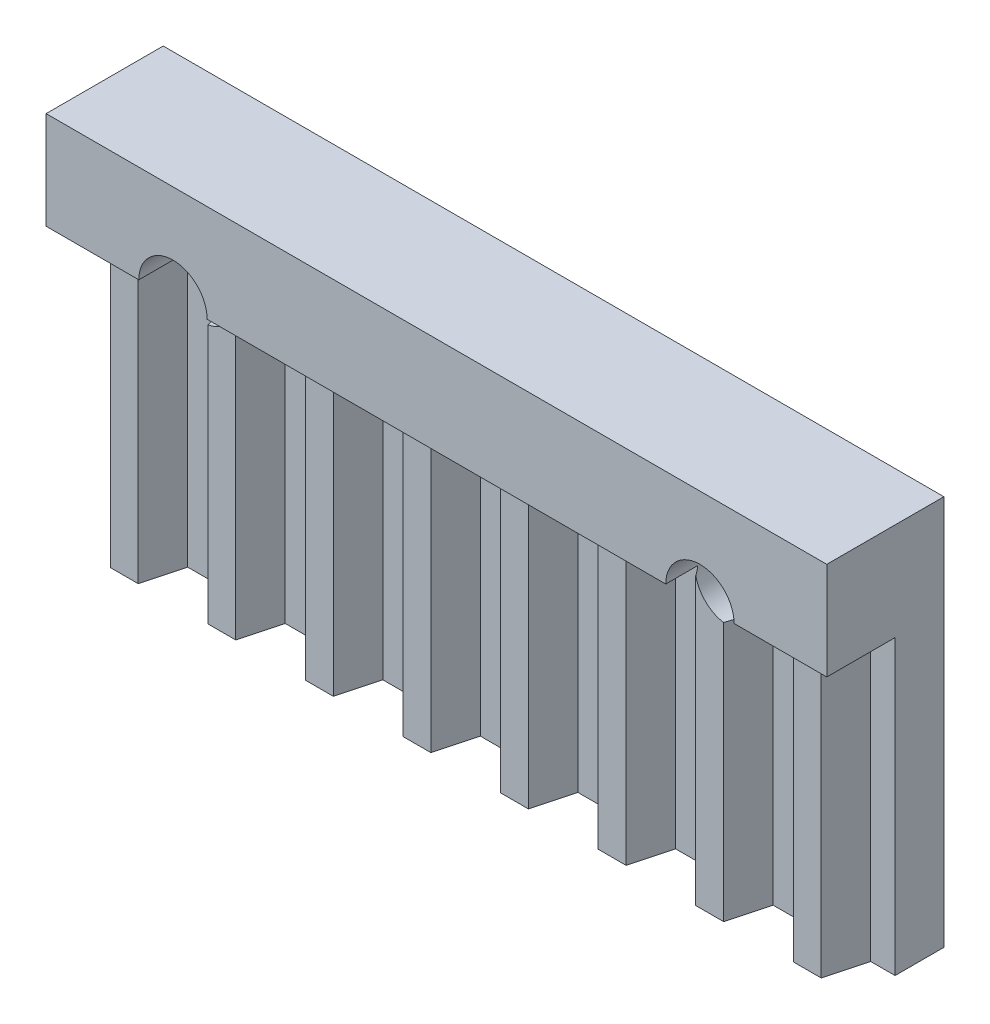
SolidWorks part; units mm, degrees
ref_plane "前基準面" through (0, 0, 0) normal (0, 0, 1) x (1, 0, 0)
ref_plane "上基準面" through (0, 0, 0) normal (0, 1, 0) x (1, 0, 0)
ref_plane "右基準面" through (0, 0, 0) normal (1, 0, 0) x (0, 0, -1)
sketch "草圖1" plane through (0, 0, 0) normal (0, 0, 1) x (1, 0, 0)
  line L0 (0, -10) -> (0, 10) construction
  line L1 (-20, 10) -> (20, 10)
  line L2 (-20, 10) -> (-20, -10)
  line L3 (-20, -10) -> (20, -10)
  line L4 (20, 10) -> (20, -10)
  circle A0 centre (-13.5, 5) radius 1.75
  circle A1 centre (13.5, 5) radius 1.75
  dimension "D3" = 6.5
  dimension "D4" = 5
  dimension "D5" = 3.5
  dimension "D1" = 40
  dimension "D2" = 20
extrude "填料-伸長1" add sketch "草圖1" along normal blind 6
sketch "草圖2" plane through (0, -10, 0) normal (0, -1, 0) x (1, 0, 0)
  line L0 (20, 6) -> (20, 0) construction
  line L1 (-20, 6) -> (20, 6)
  line L2 (-20, 6) -> (-20, 4.5)
  line L3 (-20, 4.5) -> (20, 4.5)
  line L4 (20, 6) -> (20, 4.5)
  dimension "D1" = 1.5
extrude "除料-伸長1" cut sketch "草圖2" against normal blind 15
sketch "草圖3" plane through (0, -10, 0) normal (0, -1, 0) x (-1, 0, 0)
  line L0 (17.5, 0) -> (17.5, -3.4168) construction
  line L1 (20, -4.5) -> (18.2141, -4.5)
  line L2 (20, -4.5) -> (20, -2.5)
  line L3 (20, -2.5) -> (18.75, -2.5)
  line L4 (18.2141, -4.5) -> (18.75, -2.5)
  line L5 (20, 0) -> (-20, 0) construction
  line L6 (16.7859, -4.5) -> (16.25, -2.5)
  line L7 (15, -2.5) -> (16.25, -2.5)
  line L8 (15, -4.5) -> (15, -2.5)
  line L9 (15, -4.5) -> (16.7859, -4.5)
  dimension "D1" = 75
  dimension "D2" = 2
  dimension "D3" = 5
  dimension "D4" = 2.5
extrude "除料-伸長2" cut sketch "草圖3" against normal up to surface (15 mm away) up to face at (-17.625, 5, 5.25)
pattern_linear "直線複製排列1" count 8 spacing 5 along (1, 0, 0) of "除料-伸長2"
